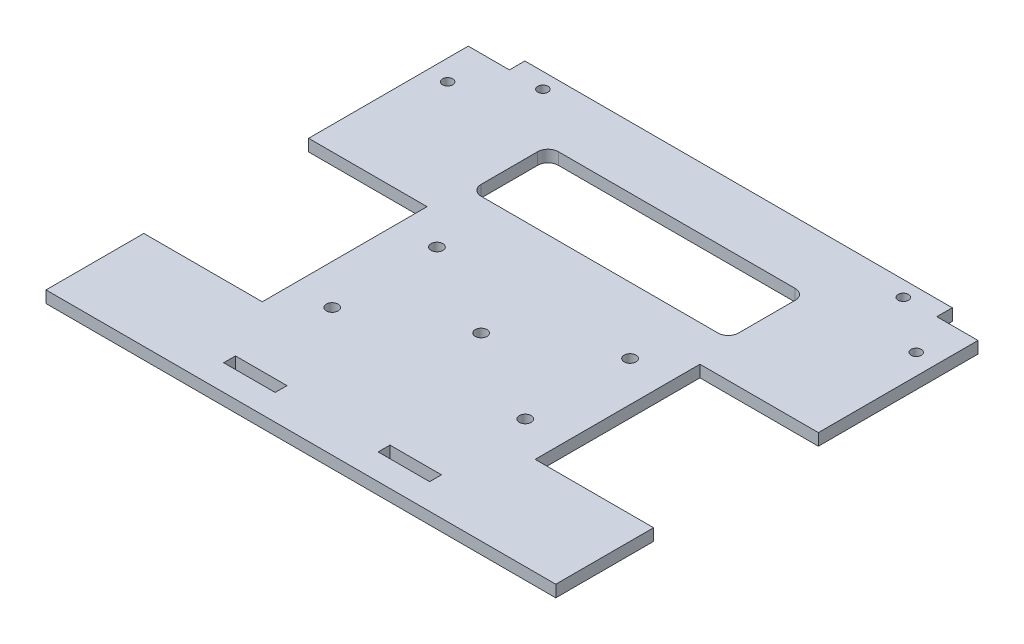
SolidWorks part; units mm, degrees
ref_plane "Front Plane" through (0, 0, 0) normal (0, 0, 1) x (1, 0, 0)
ref_plane "Top Plane" through (0, 0, 0) normal (0, 1, 0) x (1, 0, 0)
ref_plane "Right Plane" through (0, 0, 0) normal (1, 0, 0) x (0, 0, -1)
sketch "Sketch2" plane through (0, 0, 0) normal (0, 1, 0) x (1, 0, 0)
  line L0 (0, 0) -> (49.5, 0) construction
  line L1 (0, 0) -> (-49.5, 0) construction
  line L2 (0, 0) -> (0, 35) construction
  line L3 (0, 0) -> (0, -50) construction
  line L4 (0, 35) -> (-49.5, 35)
  line L5 (-49.5, 35) -> (-49.5, 0)
  line L6 (-49.5, 0) -> (-49.5, -50)
  line L7 (-49.5, -50) -> (0, -50)
  line L8 (0, -50) -> (49.5, -50)
  line L9 (49.5, -50) -> (49.5, 0)
  line L10 (49.5, 0) -> (49.5, 35)
  line L11 (49.5, 35) -> (0, 35)
  dimension "D1" = 49.5
  dimension "D2" = 49.5
  dimension "D3" = 35
  dimension "D4" = 50
extrude "Boss-Extrude1" add sketch "Sketch2" along normal blind 2.3
sketch "Sketch3" plane through (0, 2.3, 0) normal (0, 1, 0) x (1, 0, 0)
  line L0 (-49.5, 35) -> (-49.5, 32) construction
  line L1 (-49.5, 35) -> (-49.5, -50) construction
  line L2 (-49.5, 35) -> (-41.5, 35) construction
  line L3 (49.5, 35) -> (-49.5, 35) construction
  line L4 (-49.5, 32) -> (-41.5, 32)
  line L5 (-41.5, 32) -> (-41.5, 35)
  line L6 (-41.5, 35) -> (-49.5, 35)
  line L7 (-49.5, 35) -> (-49.5, 32)
  line L8 (-49.5, 32) -> (49.5, 32) construction
  line L9 (49.5, -50) -> (49.5, 35) construction
  line L10 (49.5, 35) -> (41.5, 35)
  line L11 (41.5, 35) -> (41.5, 32)
  line L12 (41.5, 32) -> (49.5, 32)
  line L13 (49.5, 32) -> (49.5, 35)
  line L14 (0, 0) -> (0, -15) construction
  line L15 (0, -15) -> (-49.5, -15) construction
  line L16 (0, -15) -> (49.5, -15) construction
  line L17 (-49.5, -15) -> (-49.5, -31) construction
  line L18 (-49.5, -15) -> (-49.5, 1) construction
  line L19 (-49.5, 1) -> (49.5, 1) construction
  line L20 (-49.5, -31) -> (49.5, -31) construction
  line L21 (49.5, 1) -> (26.5, 1)
  line L22 (26.5, 1) -> (26.5, -31)
  line L23 (26.5, -31) -> (49.5, -31)
  line L24 (49.5, -31) -> (49.5, 1)
  line L25 (-49.5, 1) -> (-26.5, 1)
  line L26 (-26.5, 1) -> (-26.5, -31)
  line L27 (-26.5, -31) -> (-49.5, -31)
  line L28 (-49.5, -31) -> (-49.5, 1)
  dimension "D1" = 3
  dimension "D2" = 8
  dimension "D3" = 8
  dimension "D4" = 15
  dimension "D5" = 16
  dimension "D6" = 16
  dimension "D7" = 23
  dimension "D8" = 23
extrude "Cut-Extrude1" cut sketch "Sketch3" against normal through all
sketch "Sketch4" plane through (0, 2.3, 0) normal (0, 1, 0) x (1, 0, 0)
  line L0 (-45.5, 32) -> (-45.5, 24) construction
  line L1 (-49.5, 32) -> (-41.5, 32) construction
  line L2 (45.5, 32) -> (45.5, 24) construction
  line L3 (41.5, 32) -> (49.5, 32) construction
  circle A0 centre (-45.5, 24) radius 1
  circle A1 centre (45.5, 24) radius 1
  dimension "D3" = 2
  dimension "D1" = 8
  dimension "D2" = 8
extrude "Cut-Extrude2" cut sketch "Sketch4" against normal through all
sketch "Sketch6" plane through (0, 2.3, 0) normal (0, 1, 0) x (1, 0, 0)
  line L0 (-26.5, -15) -> (26.5, -15) construction
  line L1 (-26.5, -31) -> (-26.5, 1) construction
  line L2 (26.5, 1) -> (26.5, -31) construction
  line L3 (26.5, -15) -> (26.5, -25.175) construction
  line L4 (26.5, -15) -> (26.5, -4.825) construction
  line L5 (26.5, -4.825) -> (-26.5, -4.825) construction
  line L6 (26.5, -25.175) -> (-26.5, -25.175) construction
  line L7 (0, -4.825) -> (-18.75, -4.825) construction
  line L8 (-18.75, -4.825) -> (-18.75, -25.175) construction
  line L9 (0, -4.825) -> (0, -25.175) construction
  line L10 (0, -4.825) -> (18.75, -4.825) construction
  line L11 (18.75, -4.825) -> (18.75, -25.175) construction
  circle A0 centre (0, -15) radius 1.15
  circle A1 centre (-18.75, -4.825) radius 1.15
  circle A2 centre (-18.75, -25.175) radius 1.15
  circle A3 centre (18.75, -4.825) radius 1.15
  circle A4 centre (18.75, -25.175) radius 1.15
  dimension "D5" = 2.3
  dimension "D1" = 10.175
  dimension "D2" = 10.175
  dimension "D3" = 18.75
  dimension "D4" = 18.75
extrude "Cut-Extrude3" cut sketch "Sketch6" against normal through all
sketch "Sketch8" plane through (0, 2.3, 0) normal (0, 1, 0) x (1, 0, 0)
  line L0 (0, 35) -> (-35, 35) construction
  line L1 (41.5, 35) -> (-41.5, 35) construction
  line L2 (0, 35) -> (35, 35) construction
  line L3 (-35, 35) -> (-35, 32) construction
  line L4 (35, 35) -> (35, 32) construction
  circle A0 centre (-35, 32) radius 1
  circle A1 centre (35, 32) radius 1
  dimension "D5" = 2
  dimension "D1" = 35
  dimension "D2" = 35
  dimension "D3" = 3
  dimension "D4" = 3
extrude "Cut-Extrude4" cut sketch "Sketch8" against normal through all
sketch "Sketch9" plane through (0, 2.3, 0) normal (0, 1, 0) x (1, 0, 0)
  line L0 (-49.5, -50) -> (-49.5, -45) construction
  line L1 (-49.5, -31) -> (-49.5, -50) construction
  line L2 (-49.5, -45) -> (-49.5, -42.7) construction
  line L3 (-49.5, -45) -> (49.5, -45) construction
  line L4 (49.5, -50) -> (49.5, -31) construction
  line L5 (-49.5, -42.7) -> (49.5, -42.7) construction
  line L6 (0, -45) -> (-10, -45) construction
  line L7 (-10, -45) -> (-20, -45)
  line L8 (-20, -45) -> (-20, -42.7)
  line L9 (-20, -42.7) -> (-10, -42.7)
  line L10 (-10, -42.7) -> (-10, -45)
  line L11 (0, -45) -> (10, -45) construction
  line L12 (10, -45) -> (20, -45)
  line L13 (10, -45) -> (10, -42.7)
  line L14 (10, -42.7) -> (20, -42.7)
  line L15 (20, -42.7) -> (20, -45)
  dimension "D1" = 5
  dimension "D2" = 2.3
  dimension "D3" = 10
  dimension "D4" = 10
  dimension "D5" = 10
  dimension "D6" = 10
extrude "Cut-Extrude5" cut sketch "Sketch9" against normal blind 2.3
sketch "Sketch10" plane through (0, 2.3, 0) normal (0, 1, 0) x (1, 0, 0)
  line L0 (0, 0) -> (0, 8) construction
  line L1 (0, 8) -> (25, 8)
  line L2 (0, 8) -> (-25, 8)
  line L3 (25, 8) -> (25, 23)
  line L4 (25, 23) -> (-25, 23)
  line L5 (-25, 23) -> (-25, 8)
  dimension "D1" = 8
  dimension "D2" = 25
  dimension "D3" = 25
  dimension "D4" = 15
extrude "Cut-Extrude6" cut sketch "Sketch10" against normal blind 2.3
fillet "Fillet1" radius 2 4 edges at (-25, 1.15, -23) (25, 1.15, -8) (25, 1.15, -23) (-25, 1.15, -8)
